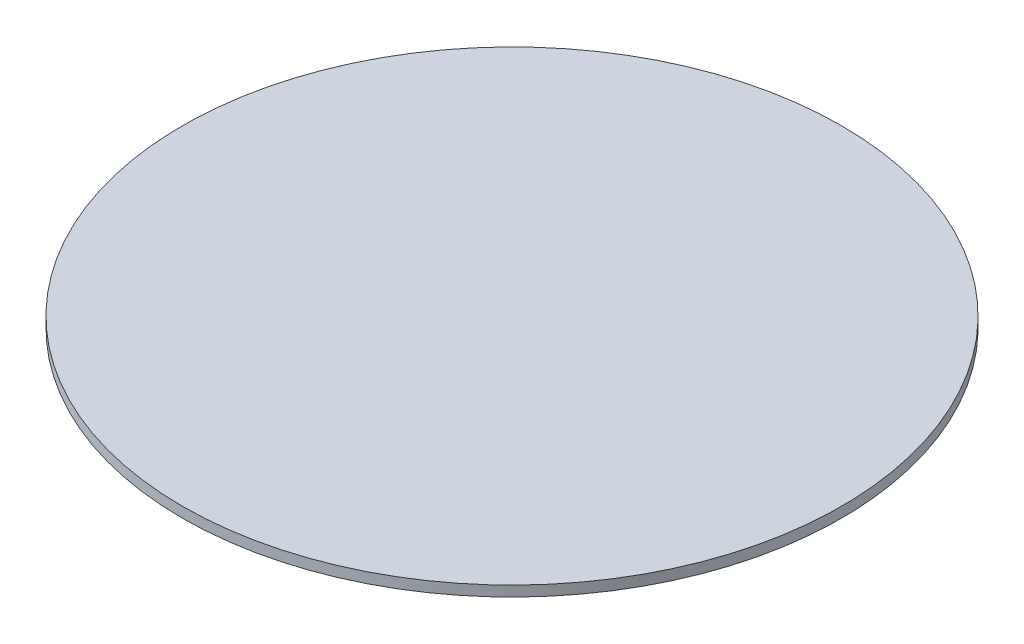
SolidWorks part; units mm, degrees
ref_plane "Front Plane" through (0, 0, 0) normal (0, 0, 1) x (1, 0, 0)
ref_plane "Top Plane" through (0, 0, 0) normal (0, 1, 0) x (1, 0, 0)
ref_plane "Right Plane" through (0, 0, 0) normal (1, 0, 0) x (0, 0, -1)
sketch "Sketch1" plane through (0, 0, 0) normal (0, 1, 0) x (1, 0, 0)
  circle A0 centre (0, 0) radius 158.75
  dimension "D1" = 317.5
extrude "Boss-Extrude1" add sketch "Sketch1" along normal blind 5
